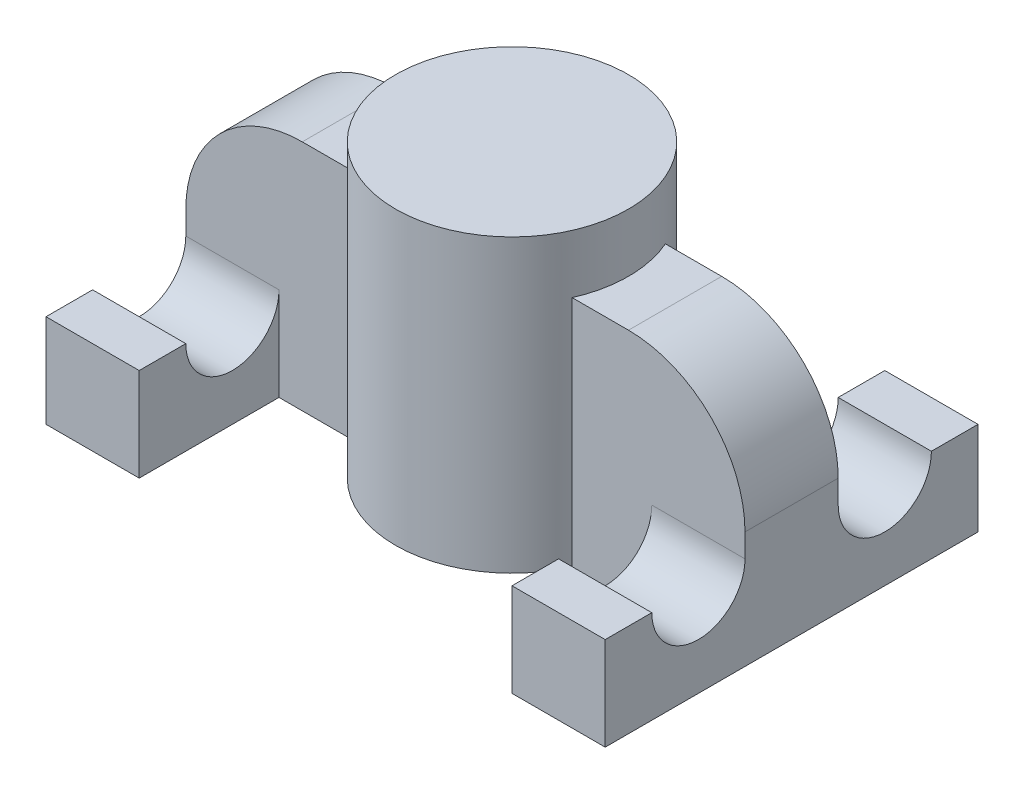
SolidWorks part; units mm, degrees
ref_plane "Front Plane" through (0, 0, 0) normal (0, 0, 1) x (1, 0, 0)
ref_plane "Top Plane" through (0, 0, 0) normal (0, 1, 0) x (1, 0, 0)
ref_plane "Right Plane" through (0, 0, 0) normal (1, 0, 0) x (0, 0, -1)
sketch "Sketch1" plane through (0, 0, 0) normal (0, 1, 0) x (1, 0, 0)
  circle A0 centre (0, 0) radius 10
  dimension "D1" = 20
extrude "Pen Cap" add sketch "Sketch1" along normal blind 25
sketch "Sketch2" plane through (0, 0, 0) normal (0, -1, 0) x (1, 0, 0)
  line L1 (-24, 4) -> (24, 4)
  line L2 (-24, 4) -> (-24, -4)
  line L3 (-24, -4) -> (24, -4)
  line L4 (24, 4) -> (24, -4)
  point P4 (0, 4)
  point P6 (-24, 0)
  dimension "D1" = 8
  dimension "D2" = 48
extrude "Hook Structure" add sketch "Sketch2" against normal blind 20
hole_wizard "Pen Centering Hole" positions "Sketch4" profile "Sketch3" legacy
sketch "Sketch4" plane through (0, 0, 0) normal (0, -1, 0) x (1, 0, 0)
  point P0 (0, 0)
sketch "Sketch3" plane through (0, 0, 0) normal (1, 0, 0) x (0, 0, -1)
  line L0 (0, 0) -> (0, 21.25)
  line L1 (0, 21.25) -> (6.25, 15)
  line L2 (6.25, 15) -> (6.25, 0)
  line L4 (6.25, 0) -> (0, 0)
  line L6 (0, 21.25) -> (-6.25, 15) construction
  line L7 (0, -4.2442) -> (0, 117.3081) construction
  dimension "Diameter" = 12.5
  dimension "Depth" = 15
  dimension "Drill Angle" = 90
sketch "Sketch6" plane through (24, 0, 0) normal (1, 0, 0) x (0, 0, -1)
  line L0 (-4, 0) -> (-16, 0)
  line L1 (-16, 0) -> (-16, 8)
  line L2 (-16, 8) -> (-12, 8)
  line L3 (-4, 0) -> (-4, 20) construction
  line L4 (-4, 8) -> (-4, 0)
  line L5 (0, 0) -> (0, 20) construction
  line L6 (4, 20) -> (-4, 20) construction
  line L7 (4, 8) -> (4, 0)
  line L8 (16, 8) -> (12, 8)
  line L9 (16, 0) -> (16, 8)
  line L10 (4, 0) -> (16, 0)
  arc A0 (-12, 8) -> (-4, 8) centre (-8, 8) ccw
  arc A1 (12, 8) -> (4, 8) centre (8, 8) cw
  dimension "D2" = 4
  dimension "D1" = 8
  dimension "D3" = 12
extrude "Hooks" add sketch "Sketch6" against normal blind 8
mirror "Hook Mirror" about plane through (0, 0, 0) normal (1, 0, 0) of "Hooks"
fillet "Corner Dec" radius 10 2 edges at (24, 20, 0) (-24, 20, 0)
